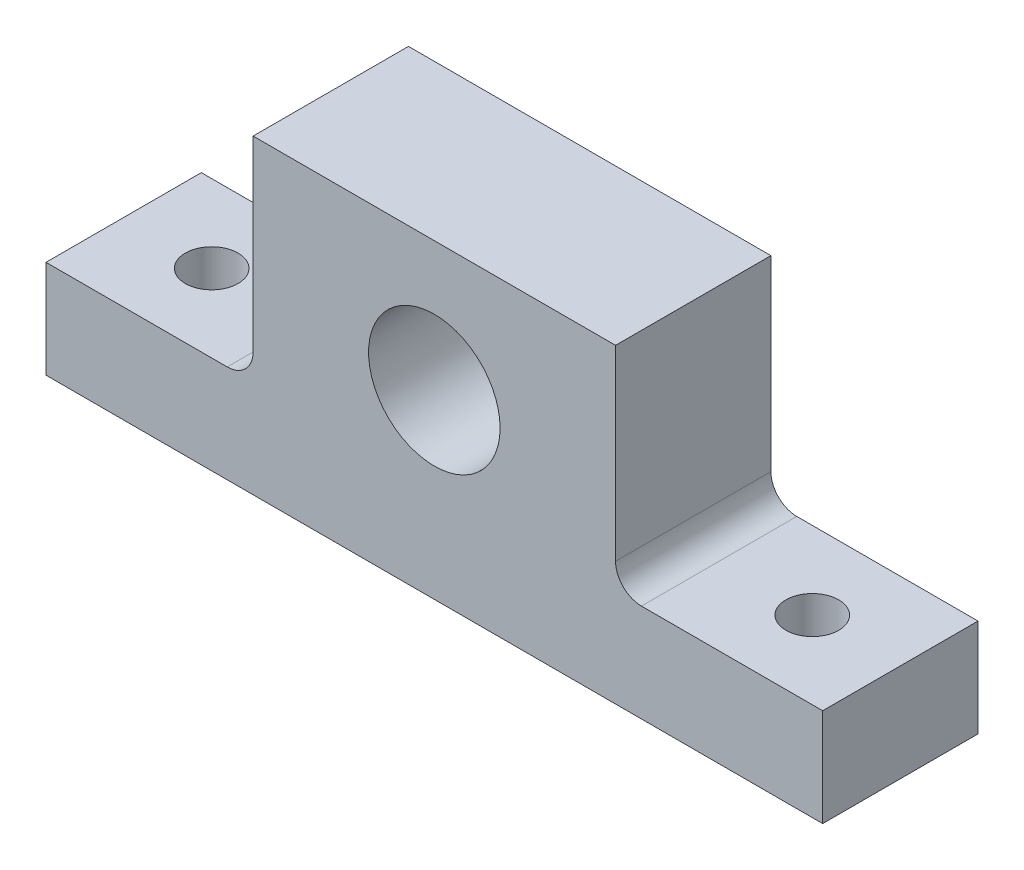
SolidWorks part; units mm, degrees
ref_plane "Front Plane" through (0, 0, 0) normal (0, 0, 1) x (1, 0, 0)
ref_plane "Top Plane" through (0, 0, 0) normal (0, 1, 0) x (1, 0, 0)
ref_plane "Right Plane" through (0, 0, 0) normal (1, 0, 0) x (0, 0, -1)
sketch "Sketch1" plane through (0, 0, 0) normal (0, 0, 1) x (1, 0, 0)
  line L0 (0, 36.5478) -> (0, -29.8483) construction
  line L1 (-75, -23.4522) -> (75, -23.4522)
  line L2 (75, -23.4522) -> (75, -4.5698)
  line L3 (75, -4.5698) -> (40, -4.5698)
  line L4 (35, 0.4302) -> (35, 36.5478)
  line L5 (35, 36.5478) -> (-35, 36.5478)
  line L6 (-75, -23.4522) -> (-75, -4.5698)
  line L7 (-75, -4.5698) -> (-40, -4.5698)
  line L8 (-35, 0.4302) -> (-35, 36.5478)
  arc A0 (40, -4.5698) -> (35, 0.4302) centre (40, 0.4302) cw
  arc A1 (-40, -4.5698) -> (-35, 0.4302) centre (-40, 0.4302) ccw
  point P11 (0, -23.4522)
  dimension "D1" = 5
  dimension "D2" = 75
  dimension "D3" = 35
  dimension "D4" = 60
extrude "Boss-Extrude1" add sketch "Sketch1" along normal blind 30
sketch "Sketch2" plane through (0, 0, 30) normal (0, 0, 1) x (1, 0, 0)
  line L1 (35, 36.5478) -> (-35, 36.5478) construction
  point P0 (0, 11.5478)
  dimension "D1" = 25
hole_wizard "1 (1.0000) Dowel Hole1" positions "Sketch4" profile "Sketch5" hole size "1" standard "ANSI Inch" end condition through all
sketch "Sketch4" plane through (0, 0, 30) normal (0, 0, 1) x (1, 0, 0)
  point P0 (0, 11.5478)
sketch "Sketch5" plane through (0, 11.5478, 30) normal (1, 0, 0) x (0, -1, 0)
  line L0 (0, 0) -> (0, 30)
  line L1 (0, 30) -> (12.7, 30)
  line L2 (12.7, 30) -> (12.7, 0)
  line L5 (12.7, 0) -> (0, 0)
  line L11 (0, -6.35) -> (0, 107.95) construction
  dimension "Thru Hole Dia." = 25.4
  dimension "Thru Hole Depth" = 30
sketch "Sketch7" plane through (0, -4.5698, 0) normal (0, 1, 0) x (1, 0, 0)
  line L0 (75, -15) -> (-75, -15) construction
  line L1 (75, -30) -> (75, 0) construction
  line L2 (-75, -30) -> (-75, 0) construction
  line L5 (58, -30) -> (58, 0) construction
  line L8 (-58, -30) -> (-58, 0) construction
  point P18 (58, -15)
  point P19 (-58, -15)
  dimension "D1" = 17
  dimension "D2" = 17
hole_wizard "Tap Drill for M12x1.75 Tap1" positions "Sketch11" profile "Sketch10" hole size "M12x1.75" standard "ANSI Metric"
sketch "Sketch11" plane through (0, -4.5698, 0) normal (0, 1, 0) x (1, 0, 0)
  point P0 (58, -15)
  point P3 (-58, -15)
sketch "Sketch10" plane through (58, -4.5698, 15) normal (1, 0, 0) x (0, 0, 1)
  line L0 (0, 0) -> (0, 33.0644)
  line L1 (0, 33.0644) -> (5.1, 30)
  line L2 (5.1, 30) -> (5.1, 0)
  line L5 (5.1, 0) -> (0, 0)
  line L10 (0, 33.0644) -> (-5.1, 30) construction
  line L11 (0, -6.35) -> (0, 107.95) construction
  dimension "Hole Dia." = 10.2
  dimension "Hole Depth" = 30
  dimension "Drill Angle" = 118
